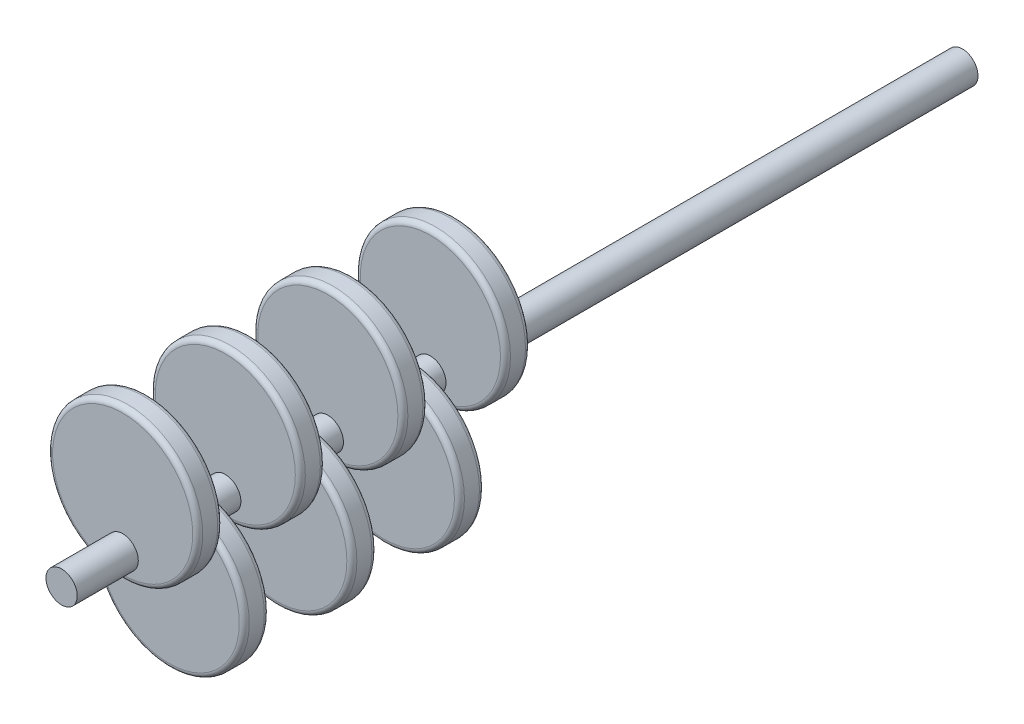
SolidWorks part; units mm, degrees
ref_plane "前视基准面" through (0, 0, 0) normal (0, 0, 1) x (1, 0, 0)
ref_plane "上视基准面" through (0, 0, 0) normal (0, 1, 0) x (1, 0, 0)
ref_plane "右视基准面" through (0, 0, 0) normal (1, 0, 0) x (0, 0, -1)
sketch "草图1" plane through (0, 0, 0) normal (0, 0, 1) x (1, 0, 0)
  circle A0 centre (0, 0) radius 3.125
  dimension "D1" = 6.25
extrude "凸台-拉伸1" add sketch "草图1" along normal mid plane 180
sketch "草图2" plane through (0, 0, 90) normal (0, 0, 1) x (1, 0, 0)
  circle A0 centre (0, 10) radius 15
  point P2 (0, 0)
  dimension "D2" = 30
  dimension "D1" = 10
extrude "凸台-拉伸2" add sketch "草图2" against normal blind 5 from offset 12.2 offset against normal yes
pattern_linear "阵列(线性)1" count 4 spacing 20.5 along (0, 0, -1) of "凸台-拉伸2"
sketch "草图3" plane through (0, 0, 90) normal (0, 0, 1) x (1, 0, 0)
  circle A0 centre (0, -10) radius 15
  dimension "D2" = 30
  dimension "D1" = 10
extrude "凸台-拉伸3" add sketch "草图3" against normal blind 5 from offset 21.5 offset against normal yes
pattern_linear "阵列(线性)2" count 3 spacing 21.5 along (0, 0, -1) of "凸台-拉伸3"
fillet "圆角1" radius 1 14 edges at (15, 10, 77.8) (15, 10, 11.3) (15, 10, 16.3) (15, -10, 20.5) (15, -10, 25.5) (15, 10, 31.8) (15, 10, 36.8) (15, -10, 42) (15, -10, 47) (15, 10, 52.3) (15, 10, 57.3) (15, -10, 63.5) (15, -10, 68.5) (15, 10, 72.8)
